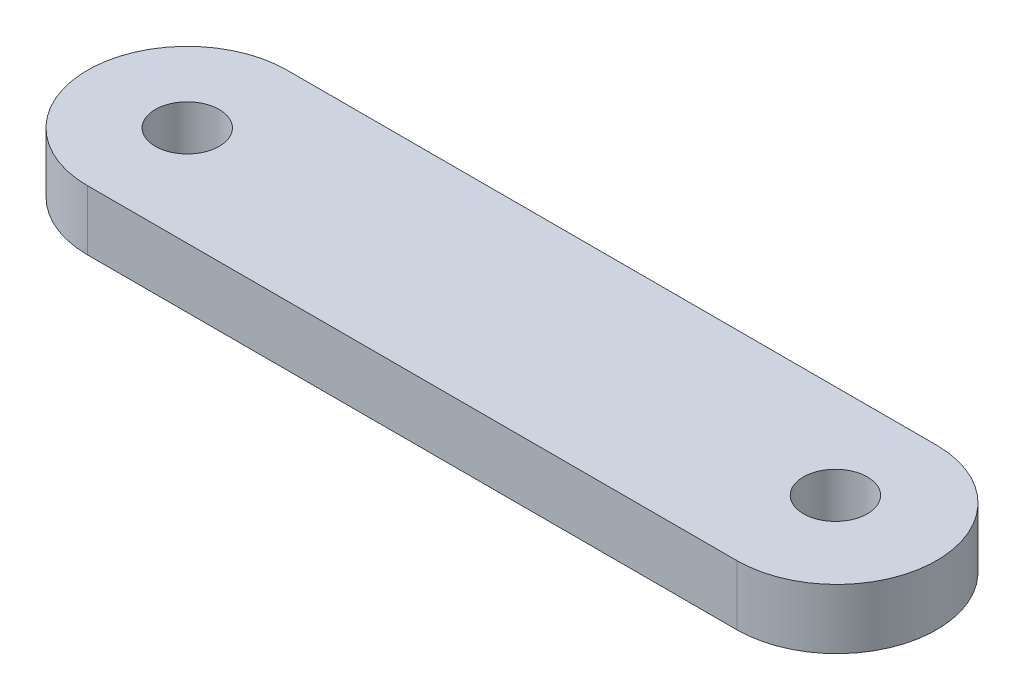
SolidWorks part; units mm, degrees
ref_plane "Front Plane" through (0, 0, 0) normal (0, 0, 1) x (1, 0, 0)
ref_plane "Top Plane" through (0, 0, 0) normal (0, 1, 0) x (1, 0, 0)
ref_plane "Right Plane" through (0, 0, 0) normal (1, 0, 0) x (0, 0, -1)
sketch "Sketch1" plane through (0, 0, 0) normal (0, 1, 0) x (1, 0, 0)
  line L0 (-37.6643, -3.875) -> (-5.1643, -3.875) construction
  line L1 (-37.6643, 1.125) -> (-5.1643, 1.125)
  line L2 (-37.6643, -8.875) -> (-5.1643, -8.875)
  arc A0 (-37.6643, 1.125) -> (-37.6643, -8.875) centre (-37.6643, -3.875) ccw
  arc A1 (-5.1643, -8.875) -> (-5.1643, 1.125) centre (-5.1643, -3.875) ccw
  circle A2 centre (-37.6643, -3.875) radius 1.6
  circle A4 centre (-5.5244, -3.5825) radius 1.6
  point P2 (-21.4143, -3.875)
  dimension "D1" = 5
  dimension "D2" = 32.5
extrude "Boss-Extrude1" add sketch "Sketch1" along normal blind 3
